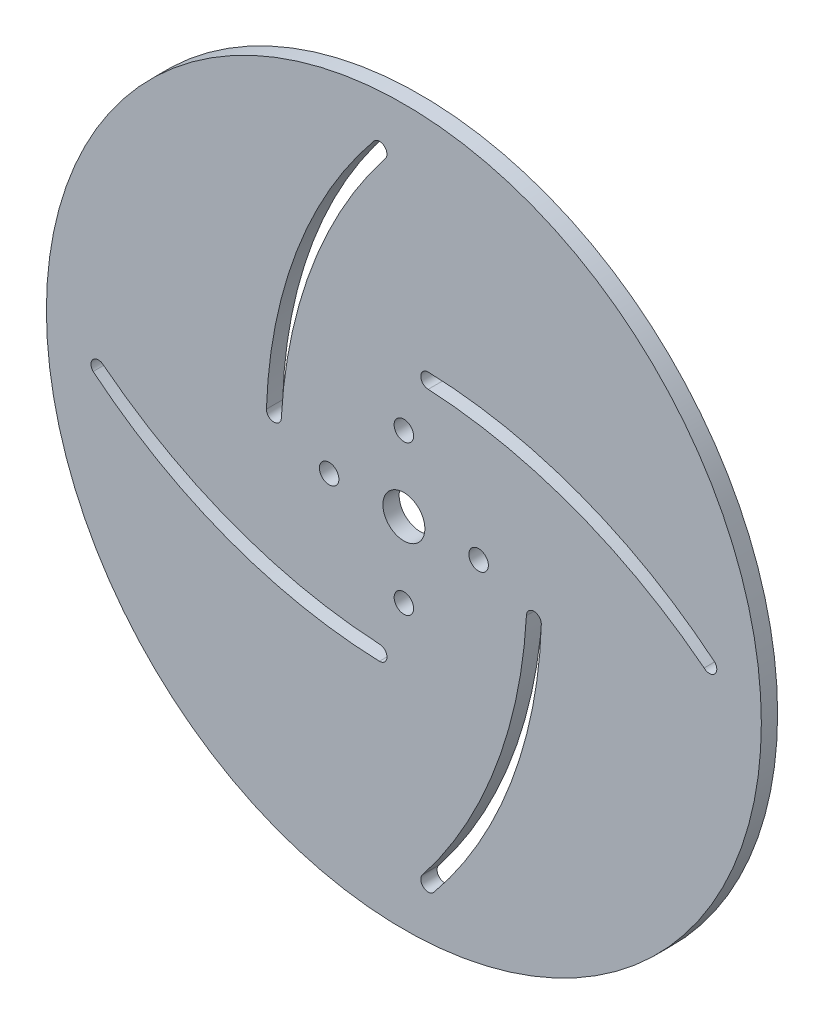
SolidWorks part; units mm, degrees
ref_plane "Front Plane" through (0, 0, 0) normal (0, 0, 1) x (1, 0, 0)
ref_plane "Top Plane" through (0, 0, 0) normal (0, 1, 0) x (1, 0, 0)
ref_plane "Right Plane" through (0, 0, 0) normal (1, 0, 0) x (0, 0, -1)
sketch "Sketch1" plane through (0, 0, 0) normal (0, 0, 1) x (1, 0, 0)
  line L0 (0, 0) -> (0, 69.85) construction
  line L1 (0, 69.85) -> (23.1636, 62.7607) construction
  line L2 (0, 0) -> (-69.85, 0) construction
  line L3 (-4.7625, 59.69) -> (-5.7884, 60.7159) construction
  line L4 (-4.7625, 59.69) -> (-3.7366, 58.6641) construction
  circle A13 centre (0, 0) radius 69.85
  circle A14 centre (0, 0) radius 4.1
  arc A42 (60.7159, 5.7884) -> (4.7776, 26.8568) centre (1.726, -66.0401) ccw
  arc A43 (4.7776, 26.8568) -> (4.7625, 23.943) centre (4.7625, 25.3999) ccw
  arc A44 (4.7625, 23.943) -> (58.6641, 3.7366) centre (-0.38, -71.7708) cw
  arc A46 (60.7159, 5.7884) -> (58.6641, 3.7366) centre (59.69, 4.7625) cw
  arc A47 (-23.943, 4.7625) -> (-3.7366, 58.6641) centre (71.7708, -0.38) cw
  arc A48 (-5.7884, 60.7159) -> (-26.8568, 4.7776) centre (66.0401, 1.726) ccw
  arc A50 (-26.8568, 4.7776) -> (-23.943, 4.7625) centre (-25.3999, 4.7625) ccw
  arc A51 (-5.7884, 60.7159) -> (-3.7366, 58.6641) centre (-4.7625, 59.69) cw
  arc A52 (5.7884, -60.7159) -> (26.8568, -4.7776) centre (-66.0401, -1.726) ccw
  arc A53 (26.8568, -4.7776) -> (23.943, -4.7625) centre (25.3999, -4.7625) ccw
  arc A54 (23.943, -4.7625) -> (3.7366, -58.6641) centre (-71.7708, 0.38) cw
  arc A55 (5.7884, -60.7159) -> (3.7366, -58.6641) centre (4.7625, -59.69) cw
  arc A56 (-60.7159, -5.7884) -> (-4.7776, -26.8568) centre (-1.726, 66.0401) ccw
  arc A57 (-4.7776, -26.8568) -> (-4.7625, -23.943) centre (-4.7625, -25.3999) ccw
  arc A58 (-4.7625, -23.943) -> (-58.6641, -3.7366) centre (0.38, 71.7708) cw
  arc A59 (-60.7159, -5.7884) -> (-58.6641, -3.7366) centre (-59.69, -4.7625) cw
  point P43 (0, 0)
  dimension "D1" = 59.69
  dimension "D2" = 4.7625
  dimension "D3" = 4
extrude "Boss-Extrude1" add sketch "Sketch1" along normal blind 3.175 contours A13
sketch "Sketch2" plane through (0, 0, 3.175) normal (0, 0, 1) x (1, 0, 0)
  arc A0 (-25.3999, 4.7625) -> (-4.7625, 59.69) centre (66.5458, 1.5573) cw
sketch "Sketch3" plane through (0, 0, 3.175) normal (0, 0, 1) x (1, 0, 0)
  line L0 (-30.1624, 4.7625) -> (-65.0875, 4.7625)
  line L1 (4.7625, 30.1624) -> (4.7625, 65.0875)
  line L2 (30.1624, -4.7625) -> (65.0875, -4.7625)
  line L3 (-4.7625, -30.1624) -> (-4.7625, -65.0875)
  arc A1 (-65.0875, 4.7625) -> (-9.525, 65.0875) centre (0.5141, 0.0905) cw
  arc A2 (-30.1624, 4.7625) -> (-9.525, 65.0875) centre (45.0213, 12.7344) cw
  arc A3 (4.7625, 30.1624) -> (65.0875, 9.525) centre (12.7344, -45.0213) cw
  arc A4 (4.7625, 65.0875) -> (65.0875, 9.525) centre (0.0905, -0.5141) cw
  arc A5 (30.1624, -4.7625) -> (9.525, -65.0875) centre (-45.0213, -12.7344) cw
  arc A6 (65.0875, -4.7625) -> (9.525, -65.0875) centre (-0.5141, -0.0905) cw
  arc A7 (-4.7625, -30.1624) -> (-65.0875, -9.525) centre (-12.7344, 45.0213) cw
  arc A8 (-4.7625, -65.0875) -> (-65.0875, -9.525) centre (-0.0905, 0.5141) cw
  point P26 (0, 0)
  dimension "D2" = 4.7625
  dimension "D3" = 4
  dimension "D1" = 4.7625
  dimension "D4" = 4.7625
  dimension "D5" = 4.7625
sketch "Sketch4" plane through (0, 0, 3.175) normal (0, 0, 1) x (1, 0, 0)
  circle A0 centre (14.605, 0) radius 1.905
  circle A1 centre (0, -14.605) radius 1.905
  circle A2 centre (-14.605, 0) radius 1.905
  circle A3 centre (0, 14.605) radius 1.905
  point P12 (0, 0)
  dimension "D1" = 14.605
  dimension "D2" = 4
extrude "Cut-Extrude1" cut sketch "Sketch4" against normal through all
equation "\"D\"= 6in"
